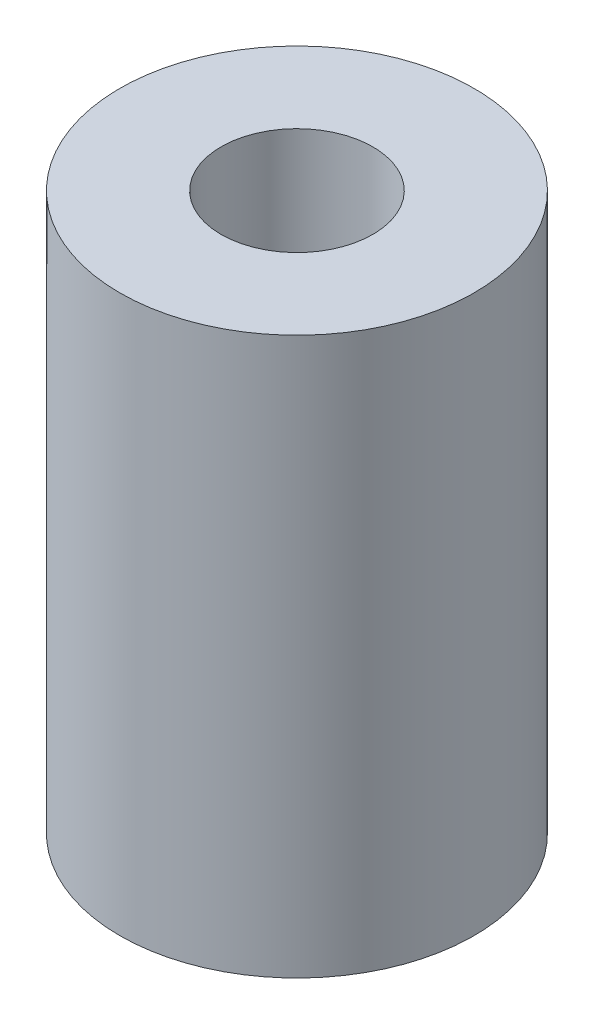
SolidWorks part; units mm, degrees
ref_plane "Front Plane" through (0, 0, 0) normal (0, 0, 1) x (1, 0, 0)
ref_plane "Top Plane" through (0, 0, 0) normal (0, 1, 0) x (1, 0, 0)
ref_plane "Right Plane" through (0, 0, 0) normal (1, 0, 0) x (0, 0, -1)
sketch "Sketch1" plane through (0, 0, 0) normal (0, 1, 0) x (1, 0, 0)
  circle A0 centre (0, 0) radius 7
  dimension "D1" = 14
extrude "Boss-Extrude1" add sketch "Sketch1" along normal mid plane 22
sketch "Sketch2" plane through (0, 11, 0) normal (0, 1, 0) x (1, 0, 0)
  circle A0 centre (0, 0) radius 3
  dimension "D1" = 6
extrude "Cut-Extrude1" cut sketch "Sketch2" against normal blind 11
sketch "Sketch3" plane through (0, -11, 0) normal (0, -1, 0) x (1, 0, 0)
  circle A0 centre (0, 0) radius 4
  dimension "D1" = 8
extrude "Cut-Extrude2" cut sketch "Sketch3" against normal blind 11
